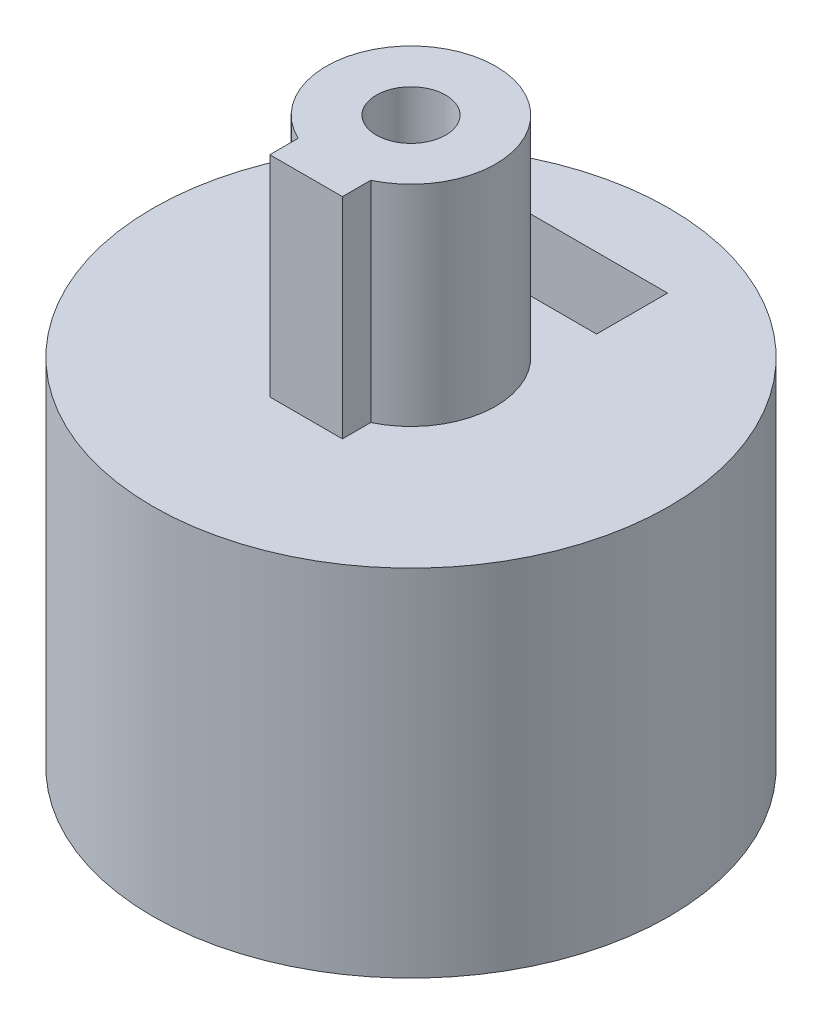
SolidWorks part; units mm, degrees
ref_plane "Front Plane" through (0, 0, 0) normal (0, 0, 1) x (1, 0, 0)
ref_plane "Top Plane" through (0, 0, 0) normal (0, 1, 0) x (1, 0, 0)
ref_plane "Right Plane" through (0, 0, 0) normal (1, 0, 0) x (0, 0, -1)
sketch "Sketch1" plane through (0, 0, 0) normal (0, 1, 0) x (1, 0, 0)
  circle A0 centre (0, 0) radius 1.965 construction
  circle A1 centre (0, 0) radius 8
  dimension "D1" = 3.93
  dimension "D2" = 16
extrude "Boss-Extrude1" add sketch "Sketch1" along normal blind 10
sketch "Sketch2" plane through (0, 0, 0) normal (0, 0, 1) x (1, 0, 0)
  line L0 (0, 10) -> (0, 0) construction
  line L1 (8, 10) -> (-8, 10) construction
  circle A0 centre (0, 7) radius 1.075
  dimension "D1" = 2.15
  dimension "D2" = 3
extrude "Cut-Extrude1" cut sketch "Sketch2" against normal through all
sketch "Sketch4" plane through (0, 0, 0) normal (0, 1, 0) x (1, 0, 0)
  circle A0 centre (0, 0) radius 2.275
  dimension "D1" = 4.55
extrude "Cut-Extrude4" cut sketch "Sketch4" along normal through all
sketch "Sketch7" plane through (0, 10, 0) normal (0, 1, 0) x (1, 0, 0)
  circle A0 centre (0, 0) radius 8
  circle A1 centre (0, 0) radius 8 construction
extrude "Boss-Extrude3" add sketch "Sketch7" along normal blind 1
sketch "Sketch8" plane through (0, 11, 0) normal (0, 1, 0) x (1, 0, 0)
  line L0 (0, 0) -> (0, -8) construction
  line L2 (-1.125, -2) -> (1.125, -2)
  line L3 (-1.125, -2) -> (-1.125, -3.25)
  line L4 (-1.125, -3.25) -> (1.125, -3.25)
  line L5 (1.125, -2) -> (1.125, -3.25)
  line L6 (0, -3.25) -> (0, -2) construction
  line L7 (-1.125, -2.625) -> (1.125, -2.625) construction
  circle A0 centre (0, 0) radius 2.625
  circle A1 centre (0, 0) radius 8 construction
  point P3 (0, -2.625)
  dimension "D1" = 5.25
  dimension "D2" = 3.25
  dimension "D3" = 2.25
extrude "Boss-Extrude4" add sketch "Sketch8" along normal blind 6.5 contours A0 L3 L4 L5
sketch "Sketch9" plane through (0, 17.5, 0) normal (0, 1, 0) x (1, 0, 0)
  circle A0 centre (0, 0) radius 1.075
  dimension "D1" = 2.15
extrude "Cut-Extrude5" cut sketch "Sketch9" against normal blind 6
sketch "Sketch3" plane through (0, 0, 0) normal (0, 0, 1) x (1, 0, 0)
  line L1 (0, 4.4019) -> (2.25, 5.701)
  line L2 (2.25, 5.701) -> (2.25, 8.299)
  line L3 (2.25, 8.299) -> (0, 9.5981) construction
  line L4 (0, 9.5981) -> (-2.25, 8.299) construction
  line L5 (-2.25, 8.299) -> (-2.25, 5.701)
  line L6 (-2.25, 5.701) -> (0, 4.4019)
  line L10 (-2.25, 8.299) -> (2.25, 8.299) construction
  line L11 (-2.25, 8.299) -> (-2.25, 11.4728)
  line L12 (2.25, 8.299) -> (2.25, 11.4728)
  line L13 (-2.25, 11.4728) -> (2.25, 11.4728)
  circle A0 centre (0, 7) radius 2.25 construction
  dimension "D1" = 4.5
extrude "Cut-Extrude2" cut sketch "Sketch3" against normal blind 2.2 from offset 3.5 offset against normal yes
sketch "Sketch10" plane through (0, 0, 0) normal (0, -1, 0) x (1, 0, 0)
  line L1 (-2.0597, 3.3482) -> (1.9328, 3.3482)
  line L2 (-2.0597, 3.3482) -> (-2.0597, 1.2)
  line L3 (-2.0597, 1.2) -> (1.9328, 1.2)
  line L4 (1.9328, 3.3482) -> (1.9328, 1.2)
  line L5 (-0.0634, 1.2) -> (-0.0634, 3.3482) construction
  line L6 (-2.0597, 2.2741) -> (1.9328, 2.2741) construction
  circle A0 centre (0, 0) radius 2.275 construction
  point P0 (-0.0634, 2.2741)
  dimension "D1" = 1.2
extrude "Boss-Extrude5" add sketch "Sketch10" against normal up to surface (10 mm away) up to face at (0, 10, 2.275)
